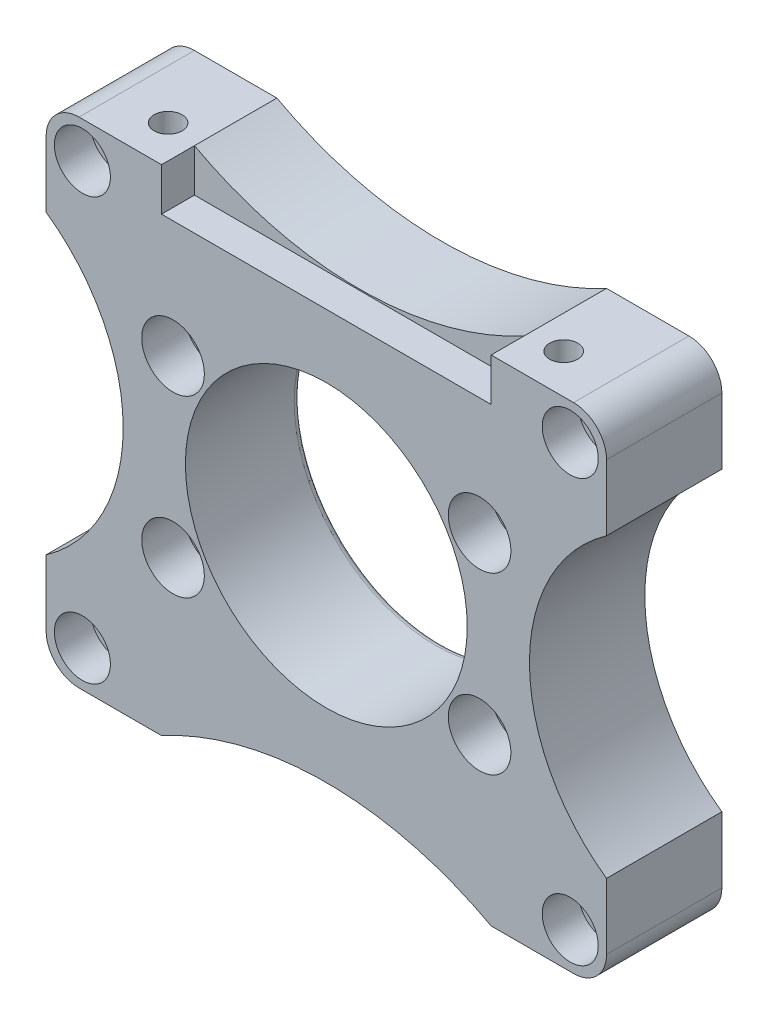
SolidWorks part; units mm, degrees
ref_plane "Plan de face" through (0, 0, 0) normal (0, 0, 1) x (1, 0, 0)
ref_plane "Plan de dessus" through (0, 0, 0) normal (0, 1, 0) x (1, 0, 0)
ref_plane "Plan de droite" through (0, 0, 0) normal (1, 0, 0) x (0, 0, -1)
sketch "Esquisse2" plane through (0, 0, 0) normal (0, 0, 1) x (1, 0, 0)
  line L1 (-170, 150) -> (0, 150)
  line L2 (-170, 150) -> (-170, 0)
  line L3 (-170, 0) -> (0, 0)
  line L4 (0, 150) -> (0, 0)
  line L5 (-170, 150) -> (0, 0) construction
  line L6 (-170, 0) -> (0, 150) construction
  point P0 (-85, 75)
  dimension "D1" = 150
  dimension "D2" = 170
extrude "Boss.-Extru.1" add sketch "Esquisse2" along normal blind 35
sketch "Esquisse3" plane through (0, 0, 35) normal (0, 0, 1) x (1, 0, 0)
  line L0 (-170, 0) -> (0, 0) construction
  line L1 (0, 0) -> (0, 150) construction
  circle A0 centre (-85, 75) radius 42.75
  point P4 (0, 75)
  dimension "D1" = 85.5
  dimension "D2" = 75
  dimension "D3" = 85
extrude "Enlèv. mat.-Extru.2" cut sketch "Esquisse3" against normal blind 40
sketch "Esquisse5" plane through (0, 0, 35) normal (0, 0, 1) x (1, 0, 0)
  line L0 (0, 150) -> (-170, 150) construction
  line L1 (-170, 0) -> (0, 0) construction
  line L2 (-170, 150) -> (-170, 0) construction
  line L3 (0, 0) -> (0, 150) construction
  circle A0 centre (-38.5, 101.5) radius 6
  circle A1 centre (-38.5, 48.5) radius 6
  circle A2 centre (-131.5, 48.5) radius 6
  circle A3 centre (-131.5, 101.5) radius 6
  dimension "D1" = 12
  dimension "D2" = 12
  dimension "D3" = 12
  dimension "D4" = 12
  dimension "D5" = 48.5
  dimension "D6" = 48.5
  dimension "D7" = 48.5
  dimension "D8" = 48.5
  dimension "D9" = 38.5
  dimension "D10" = 38.5
  dimension "D11" = 38.5
  dimension "D12" = 38.5
extrude "Enlèv. mat.-Extru.3" cut sketch "Esquisse5" against normal blind 40
sketch "Esquisse6" plane through (0, 0, 35) normal (0, 0, 1) x (1, 0, 0)
  circle A0 centre (-38.5, 101.5) radius 9.5
  circle A1 centre (-38.5, 48.5) radius 9.5
  circle A2 centre (-131.5, 48.5) radius 9.5
  circle A3 centre (-131.5, 101.5) radius 9.5
  dimension "D1" = 19
  dimension "D2" = 19
  dimension "D3" = 19
  dimension "D4" = 19
extrude "Enlèv. mat.-Extru.4" cut sketch "Esquisse6" against normal blind 13
sketch "Esquisse7" plane through (0, 0, 35) normal (0, 0, 1) x (1, 0, 0)
  line L0 (0, 150) -> (-170, 150) construction
  line L1 (0, 0) -> (0, 150) construction
  line L2 (-170, 0) -> (0, 0) construction
  line L3 (-170, 150) -> (-170, 0) construction
  circle A0 centre (-11, 139) radius 5.25
  circle A1 centre (-11, 11) radius 5.25
  circle A2 centre (-159, 11) radius 5.25
  circle A3 centre (-159, 139) radius 5.25
  dimension "D1" = 10.5
  dimension "D2" = 10.5
  dimension "D3" = 10.5
  dimension "D4" = 10.5
  dimension "D5" = 11
  dimension "D6" = 11
  dimension "D7" = 11
  dimension "D8" = 11
  dimension "D9" = 11
  dimension "D10" = 11
  dimension "D11" = 11
  dimension "D12" = 11
extrude "Enlèv. mat.-Extru.5" cut sketch "Esquisse7" against normal blind 40
sketch "Esquisse8" plane through (0, 0, 35) normal (0, 0, 1) x (1, 0, 0)
  circle A0 centre (-11, 139) radius 8.5
  circle A1 centre (-11, 11) radius 8.5
  circle A2 centre (-159, 11) radius 8.5
  circle A3 centre (-159, 139) radius 8.5
  dimension "D1" = 17
  dimension "D2" = 17
  dimension "D3" = 17
  dimension "D4" = 17
extrude "Enlèv. mat.-Extru.6" cut sketch "Esquisse8" against normal blind 11
sketch "Esquisse9" plane through (0, 150, 0) normal (0, 1, 0) x (1, 0, 0)
  line L0 (0, -35) -> (0, 0) construction
  line L1 (0, -35) -> (-170, -35) construction
  line L2 (-170, -35) -> (-170, 0) construction
  circle A0 centre (-25, -23) radius 4.25
  circle A1 centre (-145, -23) radius 4.25
  dimension "D1" = 8.5
  dimension "D2" = 8.5
  dimension "D3" = 25
  dimension "D4" = 12
  dimension "D5" = 12
  dimension "D6" = 25
extrude "Enlèv. mat.-Extru.7" cut sketch "Esquisse9" against normal blind 25
sketch "Esquisse15" plane through (0, 150, 0) normal (0, 1, 0) x (1, 0, 0)
  circle A0 centre (-145, -23) radius 5
  dimension "D1" = 10
curve "Hélice/Spirale2" pitch 1.5 height 25 turns 16.6667
sketch "Esquisse17" plane through (0, 150, 0) normal (0, 1, 0) x (1, 0, 0)
  circle A0 centre (-25, -23) radius 5
  dimension "D1" = 10
curve "Hélice/Spirale3" pitch 1.5 height 25 turns 16.6667
sketch "Esquisse19" plane through (0, 0, 35) normal (0, 0, 1) x (1, 0, 0)
  line L0 (0, 0) -> (0, 150) construction
  line L1 (0, 150) -> (-170, 150) construction
  line L2 (-170, 0) -> (0, 0) construction
  arc A0 (0, 120) -> (0, 30) centre (31.6228, 75) ccw
  dimension "D1" = 30
  dimension "D2" = 30
extrude "Enlèv. mat.-Extru.8" cut sketch "Esquisse19" against normal through all and the other way through all contours A0
sketch "Esquisse22" plane through (0, 0, 35) normal (0, 0, 1) x (1, 0, 0)
  line L0 (-170, 0) -> (0, 0) construction
  line L1 (0, 0) -> (0, 30) construction
  line L2 (-170, 150) -> (-170, 0) construction
  arc A0 (-135, 0) -> (-35, 0) centre (-85, -92.3309) cw
  dimension "D1" = 35
  dimension "D2" = 35
extrude "Enlèv. mat.-Extru.12" cut sketch "Esquisse22" against normal through all and the other way through all flip side to cut
sketch "Esquisse27" plane through (0, 0, 35) normal (0, 0, 1) x (1, 0, 0)
  line L0 (-170, 150) -> (-170, 0) construction
  line L1 (0, 150) -> (-170, 150) construction
  line L2 (-170, 0) -> (-135, 0) construction
  arc A0 (-170, 120) -> (-170, 30) centre (-201.6228, 75) cw
  dimension "D1" = 30
  dimension "D2" = 30
extrude "Enlèv. mat.-Extru.13" cut sketch "Esquisse27" against normal through all and the other way through all flip side to cut
sketch "Esquisse28" plane through (0, 0, 35) normal (0, 0, 1) x (1, 0, 0)
  line L0 (0, 150) -> (-170, 150) construction
  line L1 (0, 120) -> (0, 150) construction
  line L2 (-170, 150) -> (-170, 120) construction
  arc A0 (-135, 150) -> (-35, 150) centre (-85, 242.3309) ccw
  dimension "D1" = 35
  dimension "D2" = 35
extrude "Enlèv. mat.-Extru.14" cut sketch "Esquisse28" against normal through all and the other way through all
fillet "Congé1" radius 10 1 edges at (0, 150, 17.5)
fillet "Congé2" radius 10 1 edges at (-170, 150, 17.5)
fillet "Congé3" radius 10 1 edges at (-170, 0, 17.5)
fillet "Congé4" radius 10 1 edges at (0, 0, 17.5)
fillet "Congé5" radius 2 1 edges at (-42.25, 75, 0)
sketch "Esquisse40" plane through (0, 0, 35) normal (0, 0, 1) x (1, 0, 0)
  line L0 (-35, 150) -> (-35, 137)
  line L1 (-135, 150) -> (-135, 137)
  line L2 (-135, 137) -> (-35, 137)
  line L3 (-35, 137) -> (-35.0264, 136.9442)
  arc M17 (-35, 150) -> (-135, 150) centre (-85, 242.3309) cw
  dimension "D1" = 13
  dimension "D2" = 13
extrude "Enlèv. mat.-Extru.17" cut sketch "Esquisse40" against normal blind 10 contours L1 L2 L0 M17
